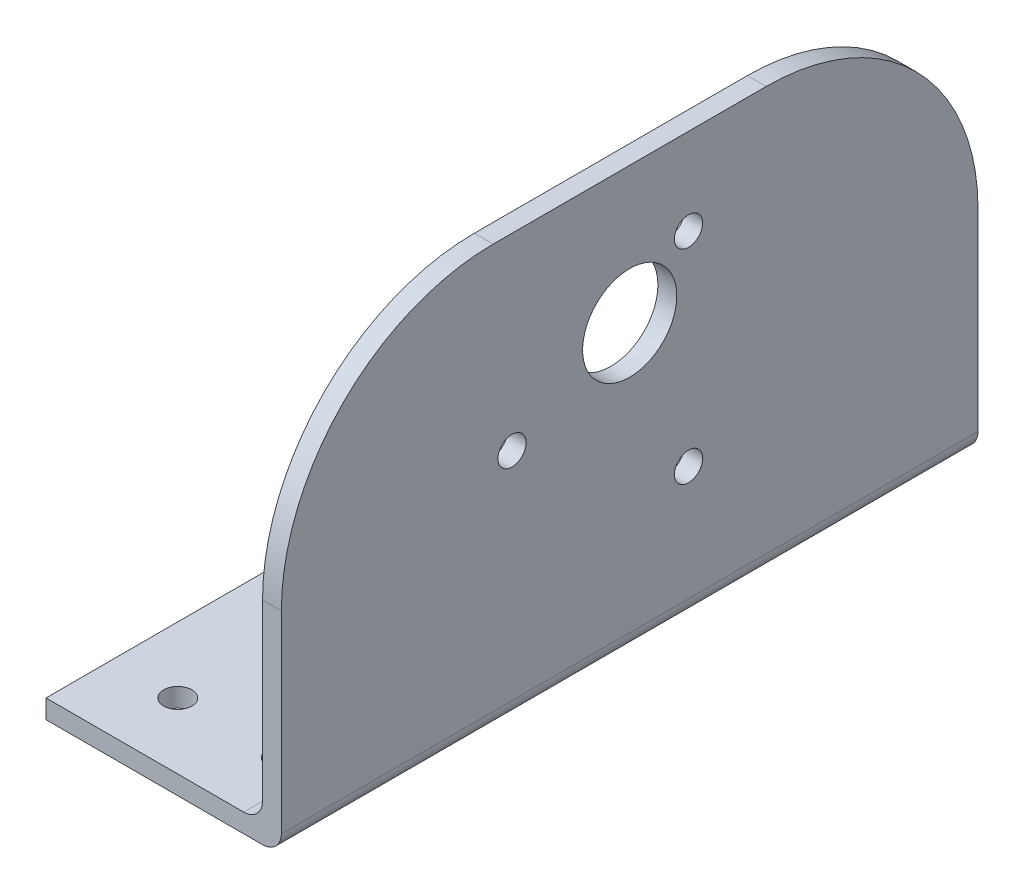
SolidWorks part; units mm, degrees
material "1060 Alloy"
ref_plane "Front Plane" through (0, 0, 0) normal (0, 0, 1) x (1, 0, 0)
ref_plane "Top Plane" through (0, 0, 0) normal (0, 1, 0) x (1, 0, 0)
ref_plane "Right Plane" through (0, 0, 0) normal (1, 0, 0) x (0, 0, -1)
sketch "Sketch1" plane through (0, 0, 0) normal (1, 0, 0) x (0, 0, -1)
  line L0 (0, 0) -> (0, 45) construction
  line L1 (-14.5, 45) -> (14.5, 45)
  line L2 (-37, 22.5) -> (-37, 0)
  line L3 (37, 22.5) -> (37, 0)
  line L4 (37, 0) -> (-37, 0)
  arc A0 (37, 22.5) -> (14.5, 45) centre (14.5, 22.5) ccw
  arc A1 (-37, 22.5) -> (-14.5, 45) centre (-14.5, 22.5) cw
  dimension "D1" = 45
  dimension "D2" = 37
  dimension "D3" = 22.5
extrude "Boss-Extrude1" add sketch "Sketch1" along normal blind 2
sketch "Sketch2" plane through (0, 0, 0) normal (-1, 0, 0) x (0, 0, 1)
  line L0 (-37, 0) -> (-37, 22.5) construction
  line L1 (37, 0) -> (-37, 0)
  line L2 (37, 0) -> (37, 2)
  line L3 (37, 2) -> (-37, 2)
  line L4 (-37, 0) -> (-37, 2)
  dimension "D1" = 2
extrude "Boss-Extrude2" add sketch "Sketch2" along normal blind 23
fillet "Fillet1" radius 2 2 edges at (2, 0, 0)
sketch "Sketch3" plane through (2, 0, 0) normal (1, 0, 0) x (0, 0, -1)
  line L0 (0, 2) -> (0, 45) construction
  line L1 (-37, 2) -> (37, 2) construction
  line L2 (14.5, 45) -> (-14.5, 45) construction
  line L3 (0, 25) -> (36.8607, 25) construction
  line L4 (0, 25) -> (6.25, 35.8253) construction
  circle A0 centre (0, 30.5) radius 5
  circle A1 centre (0, 25) radius 12.5 construction
  circle A2 centre (6.25, 35.8253) radius 1.5
  arc A3 (37, 22.5) -> (14.5, 45) centre (14.5, 22.5) ccw construction
  circle A4 centre (6.25, 14.1747) radius 1.5
  circle A5 centre (-12.5, 25) radius 1.5
  dimension "D1" = 25
  dimension "D3" = 5.5
  dimension "D4" = 3
  dimension "D6" = 10
  dimension "D2" = 25
  dimension "D5" = 60
  dimension "D7" = 3
extrude "Cut-Extrude1" cut sketch "Sketch3" against normal through all
sketch "Sketch5" plane through (0, 0, 0) normal (0, -1, 0) x (1, 0, 0)
  line L0 (-23, 0) -> (0, 0) construction
  line L1 (-23, -37) -> (-23, 37) construction
  line L2 (0, -37) -> (-23, -37) construction
  circle A0 centre (-16, -30) radius 1.5
  circle A1 centre (-5, -30) radius 1.5
  circle A2 centre (-5, 30) radius 1.5
  circle A3 centre (-16, 30) radius 1.5
  dimension "D5" = 3
  dimension "D1" = 7
  dimension "D2" = 7
  dimension "D3" = 18
  dimension "D4" = 7
extrude "Cut-Extrude2" cut sketch "Sketch5" against normal through all
